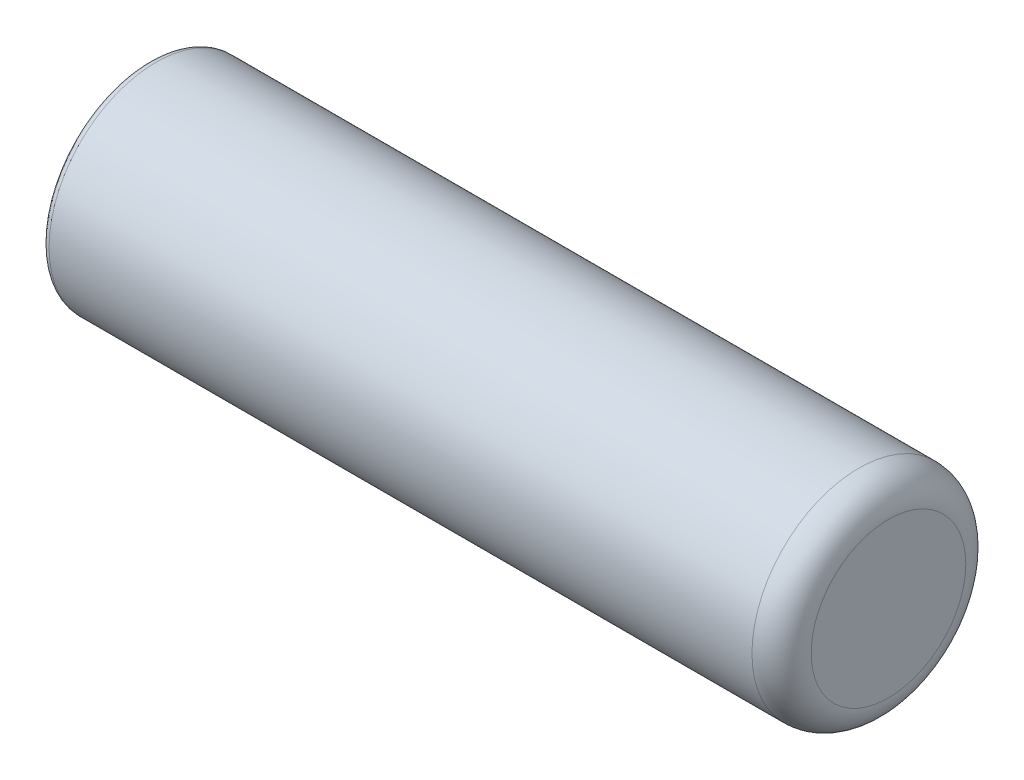
SolidWorks part; units mm, degrees
ref_plane "Front Plane" through (0, 0, 0) normal (0, 0, 1) x (1, 0, 0)
ref_plane "Top Plane" through (0, 0, 0) normal (0, 1, 0) x (1, 0, 0)
ref_plane "Right Plane" through (0, 0, 0) normal (1, 0, 0) x (0, 0, -1)
sketch "Sketch1" plane through (0, 0, 0) normal (1, 0, 0) x (0, 0, -1)
  circle A0 centre (0, 0) radius 14.45
  dimension "D2" = 28.9
extrude "Boss-Extrude1" add sketch "Sketch1" along normal blind 100
fillet "Fillet1" radius 4 1 edges at (100, 0, -14.45)
sketch "Sketch3" plane through (0, 0, 0) normal (-1, 0, 0) x (0, 0, 1)
  circle A1 centre (0, 0) radius 11
  dimension "D1" = 22
extrude "Cut-Extrude1" cut sketch "Sketch3" against normal blind 80
fillet "Fillet2" radius 1 1 edges at (0, 0, -14.45)
